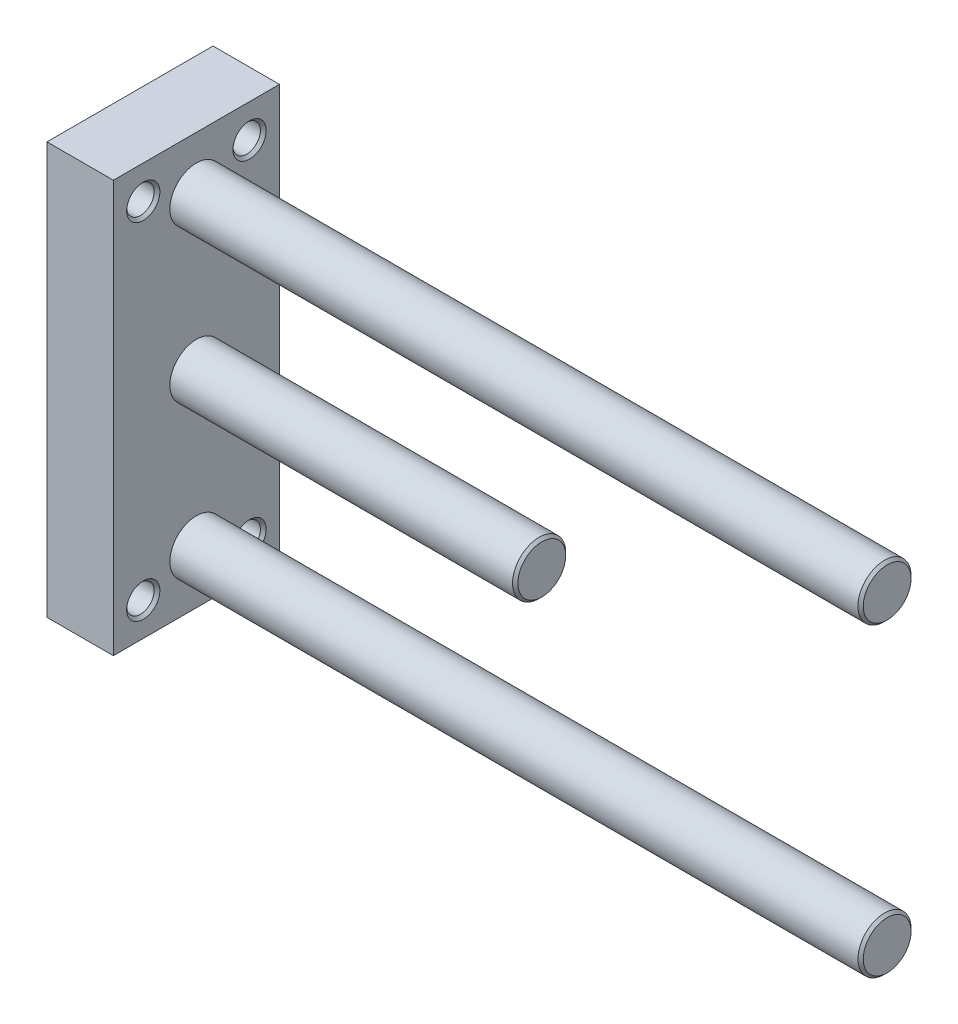
SolidWorks part; units mm, degrees
ref_plane "Front" through (0, 0, 0) normal (0, 0, 1) x (1, 0, 0)
ref_plane "Top" through (0, 0, 0) normal (0, 1, 0) x (1, 0, 0)
ref_plane "Right" through (0, 0, 0) normal (1, 0, 0) x (0, 0, -1)
ref_plane "Plane1" through (0, 0, 0) normal (1, 0, 0) x (0, 0, -1)
sketch "Sketch1" plane through (0, 0, 0) normal (1, 0, 0) x (0, 0, -1)
  line L0 (-12.5, -31) -> (12.5, -31)
  line L1 (12.5, -31) -> (12.5, 31)
  line L2 (12.5, 31) -> (-12.5, 31)
  line L3 (-12.5, 31) -> (-12.5, -31)
extrude "Boss-Extrude1" add sketch "Sketch1" along normal blind 10
ref_plane "Plane2" through (0, 26, 0) normal (0, 1, 0) x (-1, 0, 0)
sketch "Sketch2" plane through (0, 26, 0) normal (0, 1, 0) x (-1, 0, 0)
  line L0 (0, -8) -> (0, -10.5)
  line L1 (0, -10.5) -> (-0.433, -10.067)
  line L2 (-0.433, -10.067) -> (-9.567, -10.067)
  line L3 (-9.567, -10.067) -> (-10, -10.5)
  line L4 (-10, -10.5) -> (-10, -8)
  line L5 (-10, -8) -> (0, -8)
  line L6 (-10, -8) -> (0, -8) construction
revolve "Cut-Revolve1" cut sketch "Sketch2" angle 360 about L6
ref_plane "Plane3" through (0, -26, 0) normal (0, 1, 0) x (-1, 0, 0)
sketch "Sketch3" plane through (0, -26, 0) normal (0, 1, 0) x (-1, 0, 0)
  line L0 (0, -8) -> (0, -10.5)
  line L1 (0, -10.5) -> (-0.433, -10.067)
  line L2 (-0.433, -10.067) -> (-9.567, -10.067)
  line L3 (-9.567, -10.067) -> (-10, -10.5)
  line L4 (-10, -10.5) -> (-10, -8)
  line L5 (-10, -8) -> (0, -8)
  line L6 (-10, -8) -> (0, -8) construction
revolve "Cut-Revolve2" cut sketch "Sketch3" angle 360 about L6
ref_plane "Plane4" through (0, -26, 0) normal (0, 1, 0) x (-1, 0, 0)
sketch "Sketch4" plane through (0, -26, 0) normal (0, 1, 0) x (-1, 0, 0)
  line L0 (0, 8) -> (0, 5.5)
  line L1 (0, 5.5) -> (-0.433, 5.933)
  line L2 (-0.433, 5.933) -> (-9.567, 5.933)
  line L3 (-9.567, 5.933) -> (-10, 5.5)
  line L4 (-10, 5.5) -> (-10, 8)
  line L5 (-10, 8) -> (0, 8)
  line L6 (-10, 8) -> (0, 8) construction
revolve "Cut-Revolve3" cut sketch "Sketch4" angle 360 about L6
ref_plane "Plane5" through (0, 26, 0) normal (0, 1, 0) x (-1, 0, 0)
sketch "Sketch5" plane through (0, 26, 0) normal (0, 1, 0) x (-1, 0, 0)
  line L0 (0, 8) -> (0, 5.5)
  line L1 (0, 5.5) -> (-0.433, 5.933)
  line L2 (-0.433, 5.933) -> (-9.567, 5.933)
  line L3 (-9.567, 5.933) -> (-10, 5.5)
  line L4 (-10, 5.5) -> (-10, 8)
  line L5 (-10, 8) -> (0, 8)
  line L6 (-10, 8) -> (0, 8) construction
revolve "Cut-Revolve4" cut sketch "Sketch5" angle 360 about L6
ref_plane "Plane6" through (0, 23, 0) normal (0, 1, 0) x (-1, 0, 0)
sketch "Sketch6" plane through (0, 23, 0) normal (0, 1, 0) x (-1, 0, 0)
  line L0 (0, 0) -> (0, -3.8)
  line L1 (0, -3.8) -> (-5.5556, -3.8)
  line L2 (-5.5556, -3.8) -> (-5.5556, -3.5)
  line L3 (-5.5556, -3.5) -> (-2.0556, -3.5)
  line L4 (-2.0556, -3.5) -> (-1.5556, -3)
  line L5 (-1.5556, -3) -> (-1.5556, -1.5)
  line L6 (-1.5556, -1.5) -> (-4.1556, -1.5)
  line L7 (-4.1556, -1.5) -> (-5.0216, 0)
  line L8 (-5.0216, 0) -> (0, 0)
  line L9 (-5.0216, 0) -> (0, 0) construction
revolve "Cut-Revolve5" cut sketch "Sketch6" angle 360 about L9
ref_plane "Plane7" through (0, 0, 0) normal (0, 1, 0) x (-1, 0, 0)
sketch "Sketch7" plane through (0, 0, 0) normal (0, 1, 0) x (-1, 0, 0)
  line L0 (0, 0) -> (0, -3.8)
  line L1 (0, -3.8) -> (-5.5556, -3.8)
  line L2 (-5.5556, -3.8) -> (-5.5556, -3.5)
  line L3 (-5.5556, -3.5) -> (-2.0556, -3.5)
  line L4 (-2.0556, -3.5) -> (-1.5556, -3)
  line L5 (-1.5556, -3) -> (-1.5556, -1.5)
  line L6 (-1.5556, -1.5) -> (-4.1556, -1.5)
  line L7 (-4.1556, -1.5) -> (-5.0216, 0)
  line L8 (-5.0216, 0) -> (0, 0)
  line L9 (-5.0216, 0) -> (0, 0) construction
revolve "Cut-Revolve6" cut sketch "Sketch7" angle 360 about L9
ref_plane "Plane8" through (0, -23, 0) normal (0, 1, 0) x (-1, 0, 0)
sketch "Sketch8" plane through (0, -23, 0) normal (0, 1, 0) x (-1, 0, 0)
  line L0 (0, 0) -> (0, -3.8)
  line L1 (0, -3.8) -> (-5.5556, -3.8)
  line L2 (-5.5556, -3.8) -> (-5.5556, -3.5)
  line L3 (-5.5556, -3.5) -> (-2.0556, -3.5)
  line L4 (-2.0556, -3.5) -> (-1.5556, -3)
  line L5 (-1.5556, -3) -> (-1.5556, -1.5)
  line L6 (-1.5556, -1.5) -> (-4.1556, -1.5)
  line L7 (-4.1556, -1.5) -> (-5.0216, 0)
  line L8 (-5.0216, 0) -> (0, 0)
  line L9 (-5.0216, 0) -> (0, 0) construction
revolve "Cut-Revolve7" cut sketch "Sketch8" angle 360 about L9
ref_plane "Plane9" through (0, 0, 0) normal (0, 1, 0) x (-1, 0, 0)
sketch "Sketch9" plane through (0, 0, 0) normal (0, 1, 0) x (-1, 0, 0)
  line L0 (-10, 0) -> (-10, -4)
  line L1 (-10, -4) -> (-61.6, -4)
  line L2 (-61.6, -4) -> (-62, -3.6)
  line L3 (-62, -3.6) -> (-62, 0)
  line L4 (-62, 0) -> (-10, 0)
  line L5 (-62, 0) -> (-10, 0) construction
revolve "Revolve1" add sketch "Sketch9" angle 360 about L5
ref_plane "Plane10" through (0, -23, 0) normal (0, 1, 0) x (-1, 0, 0)
sketch "Sketch10" plane through (0, -23, 0) normal (0, 1, 0) x (-1, 0, 0)
  line L0 (-10, 0) -> (-10, -4)
  line L1 (-10, -4) -> (-113.6, -4)
  line L2 (-113.6, -4) -> (-114, -3.6)
  line L3 (-114, -3.6) -> (-114, 0)
  line L4 (-114, 0) -> (-10, 0)
  line L5 (-114, 0) -> (-10, 0) construction
revolve "Revolve2" add sketch "Sketch10" angle 360 about L5
ref_plane "Plane11" through (0, 23, 0) normal (0, 1, 0) x (-1, 0, 0)
sketch "Sketch11" plane through (0, 23, 0) normal (0, 1, 0) x (-1, 0, 0)
  line L0 (-10, 0) -> (-10, -4)
  line L1 (-10, -4) -> (-113.6, -4)
  line L2 (-113.6, -4) -> (-114, -3.6)
  line L3 (-114, -3.6) -> (-114, 0)
  line L4 (-114, 0) -> (-10, 0)
  line L5 (-114, 0) -> (-10, 0) construction
revolve "Revolve3" add sketch "Sketch11" angle 360 about L5
